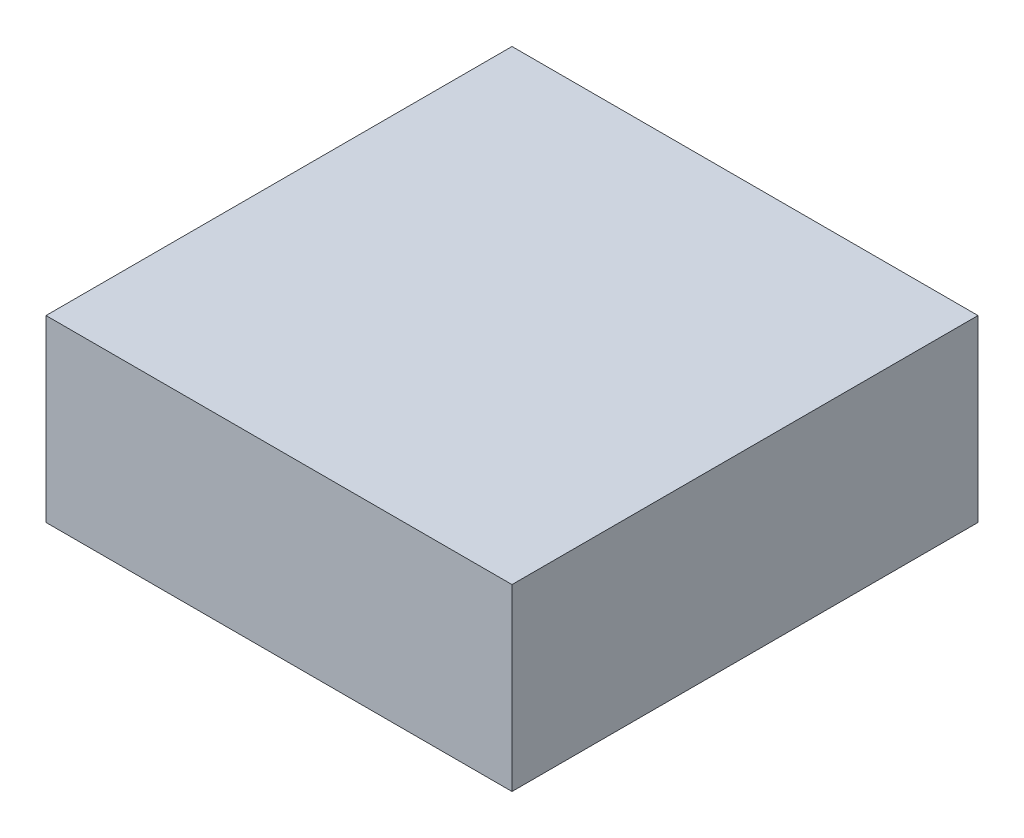
SolidWorks part; units mm, degrees
ref_plane "Front Plane" through (0, 0, 0) normal (0, 0, 1) x (1, 0, 0)
ref_plane "Top Plane" through (0, 0, 0) normal (0, 1, 0) x (1, 0, 0)
ref_plane "Right Plane" through (0, 0, 0) normal (1, 0, 0) x (0, 0, -1)
sketch "Sketch1" plane through (0, 0, 0) normal (0, 1, 0) x (1, 0, 0)
  line L1 (0, 0) -> (130, 0)
  line L2 (0, 0) -> (0, 130)
  line L3 (0, 130) -> (130, 130)
  line L4 (130, 0) -> (130, 130)
  dimension "D1" = 130
  dimension "D2" = 130
extrude "Boss-Extrude1" add sketch "Sketch1" along normal blind 50
sketch "Sketch2" plane through (0, 0, 0) normal (0, -1, 0) x (1, 0, 0)
  line L0 (130, 0) -> (130, -130) construction
  line L1 (5, -5) -> (125, -5)
  line L2 (5, -5) -> (5, -125)
  line L3 (5, -125) -> (125, -125)
  line L4 (125, -5) -> (125, -125)
  line L5 (130, -130) -> (0, -130) construction
  line L6 (0, -130) -> (0, 0) construction
  line L7 (0, 0) -> (130, 0) construction
  dimension "D1" = 5
  dimension "D2" = 5
  dimension "D3" = 5
  dimension "D4" = 5
extrude "Cut-Extrude1" cut sketch "Sketch2" against normal blind 45
sketch "Sketch3" plane through (0, 45, 0) normal (0, -1, 0) x (-1, 0, 0)
  line L0 (-125, 125) -> (-125, 5) construction
  line L2 (-5, 125) -> (-125, 125) construction
  line L3 (-5, 125) -> (-125, 125) construction
  line L4 (-125, 5) -> (-5, 5) construction
  circle A0 centre (-9, 121) radius 2.5
  circle A1 centre (-121, 121) radius 2.5
  circle A2 centre (-9, 9) radius 2.5
  circle A3 centre (-121, 9) radius 2.5
  point P6 (-121, 13.1723)
  point P7 (-9, 13.1723)
  dimension "D1" = 112
  dimension "D2" = 4
  dimension "D3" = 112
  dimension "D4" = 4
  dimension "D5" = 4
  dimension "D6" = 112
  dimension "D7" = 4
  dimension "D8" = 112
extrude "Boss-Extrude2" add sketch "Sketch3" along normal blind 5
